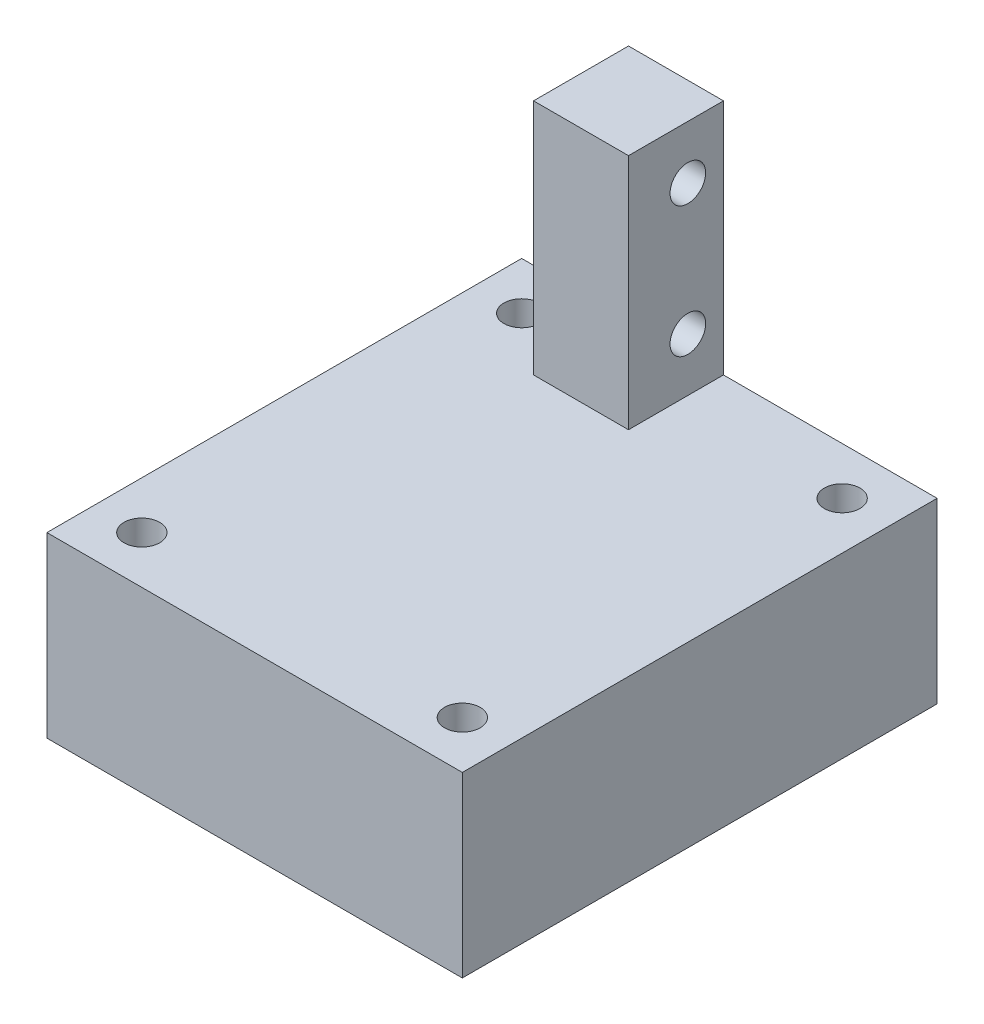
SolidWorks part; units mm, degrees
ref_plane "Front" through (0, 0, 0) normal (0, 0, 1) x (1, 0, 0)
ref_plane "Top" through (0, 0, 0) normal (0, 1, 0) x (1, 0, 0)
ref_plane "Right" through (0, 0, 0) normal (1, 0, 0) x (0, 0, -1)
sketch "Эскиз1" plane through (0, 0, 0) normal (0, 1, 0) x (1, 0, 0)
  line L5 (-17.5, 20) -> (17.5, 20)
  line L6 (-17.5, 20) -> (-17.5, -20)
  line L7 (-17.5, -20) -> (17.5, -20)
  line L8 (17.5, 20) -> (17.5, -20)
  line L9 (-17.5, 20) -> (17.5, -20) construction
  line L10 (-17.5, -20) -> (17.5, 20) construction
  point P0 (0, 0)
  dimension "D1" = 35
  dimension "D2" = 40
extrude "Бобышка-Вытянуть1" add sketch "Эскиз1" along normal blind 15
sketch "Эскиз4" plane through (0, 15, 0) normal (0, 1, 0) x (1, 0, 0)
  line L0 (-13.5, 0) -> (13.5, 0)
  line L1 (-13.5, 16) -> (13.5, 16)
  line L2 (-13.5, 16) -> (-13.5, -16)
  line L3 (-13.5, -16) -> (13.5, -16)
  line L4 (13.5, 16) -> (13.5, -16)
  line L5 (-13.5, 16) -> (13.5, -16) construction
  line L6 (-13.5, -16) -> (13.5, 16) construction
  circle A0 centre (-13.5, -16) radius 1.5
  circle A1 centre (13.5, -16) radius 1.5
  circle A2 centre (13.5, 16) radius 1.5
  circle A3 centre (-13.5, 16) radius 1.5
  point P0 (0, 0)
  dimension "D3" = 3
  dimension "D4" = 3
  dimension "D1" = 27
  dimension "D2" = 32
extrude "Вырез-Вытянуть1" cut sketch "Эскиз4" against normal blind 25 contours A3 L2 L1 | A3 L1 L2 | L4 A1 L3 | A2 L1 L4 | A2 L4 L1 | L3 A1 L4 | A0
sketch "Эскиз5" plane through (0, 15, 0) normal (0, 1, 0) x (1, 0, 0)
  line L0 (17.5, 20) -> (-17.5, 20) construction
  line L1 (-8.5, 20) -> (-0.5, 20)
  line L2 (-8.5, 20) -> (-8.5, 12)
  line L3 (-8.5, 12) -> (-0.5, 12)
  line L4 (-0.5, 20) -> (-0.5, 12)
  line L5 (17.5, -20) -> (17.5, 20) construction
  dimension "D1" = 8
  dimension "D2" = 8
  dimension "D3" = 26
extrude "Бобышка-Вытянуть2" add sketch "Эскиз5" along normal blind 20
sketch "Эскиз6" plane through (-0.5, 0, 0) normal (1, 0, 0) x (0, 0, -1)
  line L0 (-20, 15) -> (20, 15) construction
  line L1 (12, 35) -> (12, 15) construction
  line L2 (12, 35) -> (20, 35) construction
  circle A0 centre (17, 30.5) radius 1.5
  circle A1 centre (17, 19.5) radius 1.5
  dimension "D2" = 3
  dimension "D3" = 3
  dimension "D1" = 4.5
  dimension "D4" = 5
  dimension "D5" = 5
  dimension "D6" = 4.5
extrude "Вырез-Вытянуть2" cut sketch "Эскиз6" against normal blind 20
